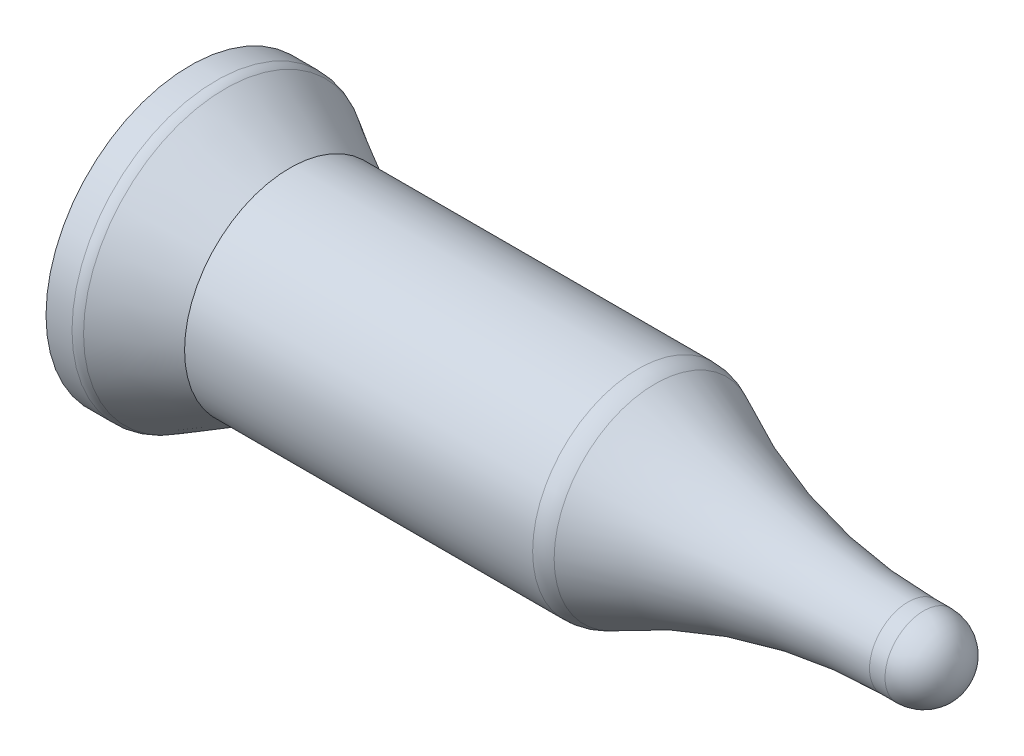
SolidWorks part; units mm, degrees
ref_plane "Front Plane" through (0, 0, 0) normal (0, 0, 1) x (1, 0, 0)
ref_plane "Top Plane" through (0, 0, 0) normal (0, 1, 0) x (1, 0, 0)
ref_plane "Right Plane" through (0, 0, 0) normal (1, 0, 0) x (0, 0, -1)
sketch "Sketch1" plane through (0, 0, 0) normal (0, 0, 1) x (1, 0, 0)
  line L16 (0, 0) -> (33.8709, 0)
  line L20 (1.4963, 5.9309) -> (1.4963, 0)
  line L24 (5.5946, 4.3307) -> (19.9095, 4.3307)
  line L25 (2.9409, 5.8321) -> (5.5946, 4.3307)
  line L26 (1.4963, 5.9309) -> (2.5657, 5.9309)
  line L27 (31.6588, -1.5875) -> (31.0211, -1.5875)
  line L28 (31.6588, 1.5875) -> (31.0211, 1.5875)
  line L29 (31.6588, 1.5875) -> (31.0211, 1.5875)
  line L30 (31.6588, -0.5715) -> (31.6588, 0.5715)
  line L31 (31.0873, 0) -> (32.2303, 0)
  arc A8 (20.6187, 4.1556) -> (31.0211, 1.5875) centre (31.0211, 23.9395) ccw
  arc A11 (2.9409, 5.8321) -> (2.5657, 5.9309) centre (2.5657, 5.1689) ccw
  arc A12 (20.6187, 4.1556) -> (19.9095, 4.3307) centre (19.9095, 2.8067) ccw
  arc A13 (33.2463, 0) -> (31.6588, 1.5875) centre (31.6588, 0) ccw
  dimension "D2" = 22.352
  dimension "D3" = 0.762
  dimension "D4" = 1.524
  dimension "D5" = 1.5875
  dimension "D1" = 14.3148
  dimension "D6" = 1.0694
  dimension "D7" = 1.4446
  dimension "D8" = 4.0983
  dimension "D9" = 19.1224
  dimension "D10" = 0.5715
  dimension "D11" = 29.591
  dimension "D12" = 30.734
  dimension "D13" = 31.75
  dimension "D14" = 32.3746
  dimension "D15" = 1.4963
  dimension "D16" = 0.5715
revolve "Revolve2" add sketch "Sketch1" angle 360 about L16
